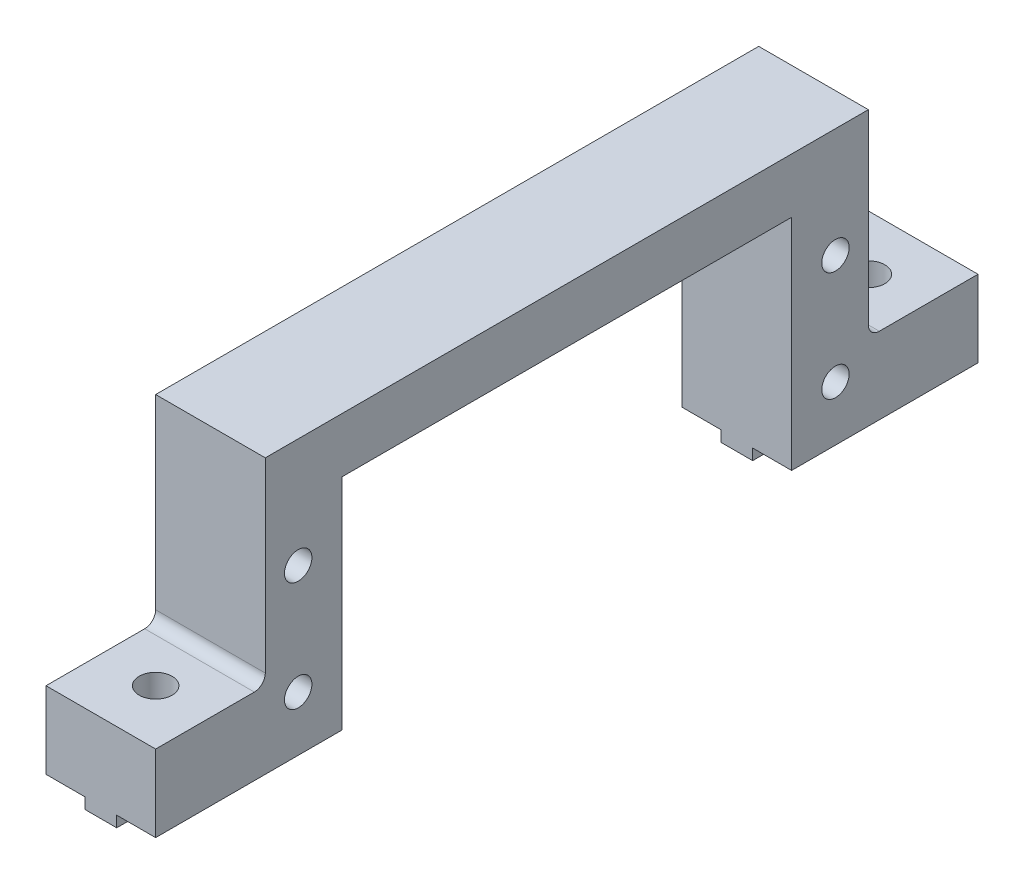
SolidWorks part; units mm, degrees
ref_plane "Front Plane" through (0, 0, 0) normal (0, 0, 1) x (1, 0, 0)
ref_plane "Top Plane" through (0, 0, 0) normal (0, 1, 0) x (1, 0, 0)
ref_plane "Right Plane" through (0, 0, 0) normal (1, 0, 0) x (0, 0, -1)
sketch "Sketch1" plane through (0, 0, 0) normal (0, 0, 1) x (1, 0, 0)
  line L0 (-5, 0) -> (-5, 25)
  line L1 (-5, 25) -> (5, 25)
  line L2 (5, 25) -> (5, 0)
  line L3 (5, 0) -> (1.45, 0)
  line L4 (1.45, 0) -> (1.45, -1)
  line L5 (1.45, -1) -> (-1.45, -1)
  line L6 (-1.45, -1) -> (-1.45, 0)
  line L7 (-1.45, 0) -> (-5, 0)
  point P2 (0, 0)
  point P11 (0, -1)
  dimension "D1" = 10
  dimension "D2" = 2.9
  dimension "D3" = 1
  dimension "D4" = 25
extrude "Main" add sketch "Sketch1" along normal mid plane 75
sketch "Sketch2" plane through (-5, 0, 0) normal (-1, 0, 0) x (0, 0, 1)
  line L0 (37.5, -1) -> (-37.5, -1) construction
  line L1 (20.5, 20) -> (-20.5, 20)
  line L2 (20.5, 20) -> (20.5, -1)
  line L3 (20.5, -1) -> (-20.5, -1)
  line L4 (-20.5, 20) -> (-20.5, -1)
  line L5 (37.5, 0) -> (-37.5, 0) construction
  point P6 (0, 20)
  point P7 (0, 0)
  dimension "D1" = 41
  dimension "D2" = 20
extrude "ServoPlace" cut sketch "Sketch2" against normal through all
sketch "Sketch3" plane through (-5, 0, 0) normal (-1, 0, 0) x (0, 0, 1)
  line L0 (-20.5, 0) -> (-37.5, 0) construction
  circle A0 centre (-24.5, 15) radius 1.25
  circle A1 centre (-24.5, 5) radius 1.25
  point P4 (0, 0)
  dimension "D1" = 2.5
  dimension "D2" = 10
  dimension "D3" = 24.5
  dimension "D4" = 5
extrude "ServoFixHole" cut sketch "Sketch3" against normal through all
mirror "ServoFixHoleMirror" about plane through (0, 0, 0) normal (0, 0, 1) of "ServoFixHole"
sketch "Sketch4" plane through (0, 25, 0) normal (0, 1, 0) x (1, 0, 0)
  line L0 (5, -37.5) -> (5, 37.5) construction
  line L1 (5, 37.5) -> (-5, 37.5)
  line L2 (5, 37.5) -> (5, 27.5)
  line L3 (5, 27.5) -> (-5, 27.5)
  line L4 (-5, 37.5) -> (-5, 27.5)
  line L5 (-5, -37.5) -> (-5, 37.5) construction
  line L7 (-5, -37.5) -> (5, -37.5)
  line L8 (-5, -37.5) -> (-5, -27.5)
  line L9 (-5, -27.5) -> (5, -27.5)
  line L10 (5, -37.5) -> (5, -27.5)
  dimension "D1" = 10
extrude "CutForFixMakerBeamHole" cut sketch "Sketch4" against normal blind 18
sketch "Sketch5" plane through (0, 7, 0) normal (0, 1, 0) x (1, 0, 0)
  line L0 (-5, -37.5) -> (5, -37.5) construction
  line L1 (5, 37.5) -> (-5, 37.5) construction
  circle A0 centre (0, 32.5) radius 1.5
  circle A1 centre (0, -32.5) radius 1.5
  point P4 (0, 0)
  dimension "D2" = 3
  dimension "D1" = 5
  dimension "D3" = 5
extrude "FixHoleMakerBeam" cut sketch "Sketch5" against normal through all
fillet "Fillet1" radius 1 2 edges at (0, 7, 27.5) (0, 7, -27.5)
